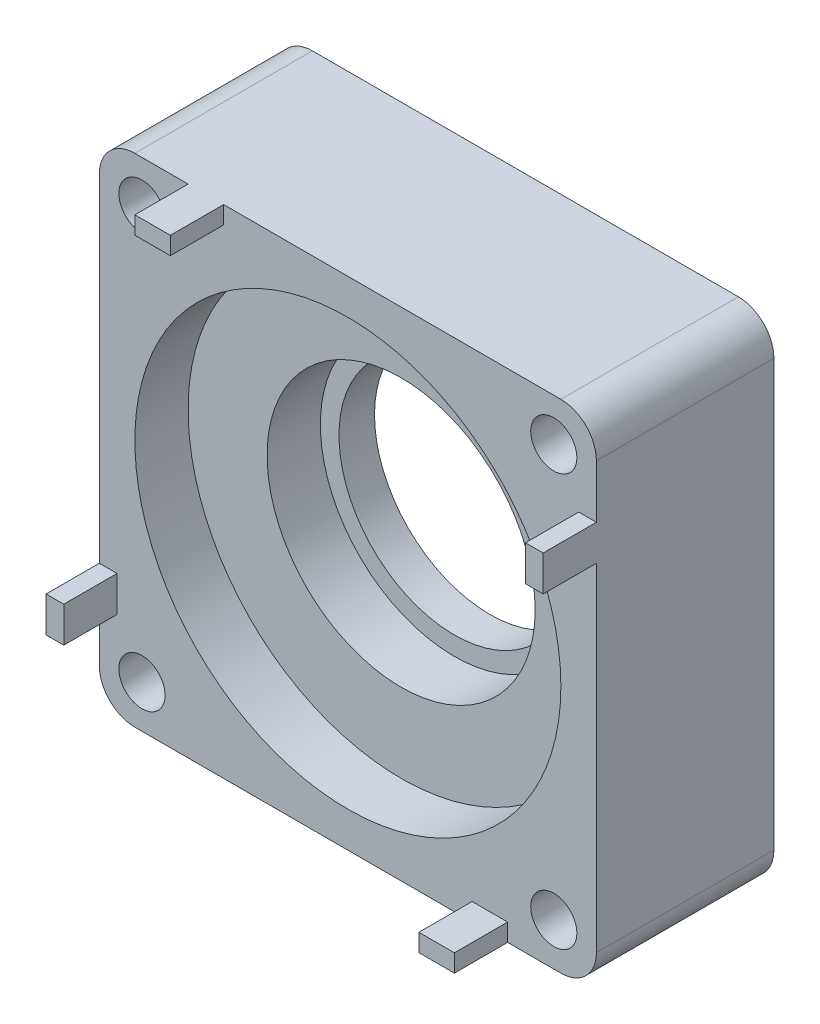
SolidWorks part; units mm, degrees
ref_plane "前视基准面" through (0, 0, 0) normal (0, 0, 1) x (1, 0, 0)
ref_plane "上视基准面" through (0, 0, 0) normal (0, 1, 0) x (1, 0, 0)
ref_plane "右视基准面" through (0, 0, 0) normal (1, 0, 0) x (0, 0, -1)
sketch "草图1" plane through (0, 0, 0) normal (0, 0, 1) x (1, 0, 0)
  line L1 (-14, 14) -> (14, 14)
  line L2 (-14, 14) -> (-14, -14)
  line L3 (-14, -14) -> (14, -14)
  line L4 (14, 14) -> (14, -14)
  line L5 (0, -14) -> (0, 14) construction
  line L6 (-14, 0) -> (14, 0) construction
  point P0 (0, 0)
  dimension "D1" = 28
  dimension "D2" = 28
extrude "凸台-拉伸1" add sketch "草图1" along normal blind 10
sketch "草图2" plane through (0, 0, 10) normal (0, 0, 1) x (1, 0, 0)
  circle A0 centre (0, 0) radius 6.5
  dimension "D1" = 13
extrude "切除-拉伸1" cut sketch "草图2" against normal through all
sketch "草图3" plane through (0, 0, 10) normal (0, 0, 1) x (1, 0, 0)
  circle A0 centre (0, 0) radius 7.55
  dimension "D1" = 15.1
extrude "切除-拉伸2" cut sketch "草图3" against normal offset from surface (6 mm away) 4 up to face at (6.5, 0, 0)
sketch "草图6" plane through (0, 0, 0) normal (0, 0, -1) x (-1, 0, 0)
  circle A0 centre (0, 0) radius 11.05
  dimension "D1" = 22.1
extrude "切除-拉伸3" cut sketch "草图6" against normal blind 2
fillet "圆角1" radius 2 4 edges at (14, -14, 5) (14, 14, 5) (-14, 14, 5) (-14, -14, 5)
sketch "草图7" plane through (0, 0, 10) normal (0, 0, 1) x (1, 0, 0)
  line L0 (-14, 12) -> (-14, -12) construction
  line L1 (-14, -7) -> (-13.0047, -7)
  line L2 (-14, -7) -> (-14, -9)
  line L3 (-14, -9) -> (-13.0047, -9)
  line L4 (-13.0047, -7) -> (-13.0047, -9)
  line L6 (-12, -14) -> (12, -14) construction
  dimension "D1" = 0.9953
  dimension "D2" = 2
  dimension "D3" = 5
extrude "凸台-拉伸2" add sketch "草图7" along normal blind 3
pattern_circular "阵列(圆周)1" count 4 over 360 about axis through (0, 0, 0) along (0, 0, 1) of "凸台-拉伸2"
sketch "草图8" plane through (0, 0, 10) normal (0, 0, 1) x (1, 0, 0)
  circle A0 centre (0, 0) radius 12
  dimension "D1" = 24
extrude "切除-拉伸4" cut sketch "草图8" against normal offset from surface (3 mm away) 3 up to face at (7.55, 0, 4)
sketch "草图9" plane through (0, 0, 0) normal (0, 0, -1) x (-1, 0, 0)
  circle A0 centre (-11.6, 11.6) radius 1.3
  circle A1 centre (11.6, 11.6) radius 1.3
  circle A2 centre (11.6, -11.6) radius 1.3
  circle A3 centre (-11.6, -11.6) radius 1.3
  point P12 (0, 0)
  dimension "D3" = 2.6
  dimension "D1" = 11.6
  dimension "D2" = 11.6
  dimension "D4" = 4
extrude "切除-拉伸5" cut sketch "草图9" against normal through all
